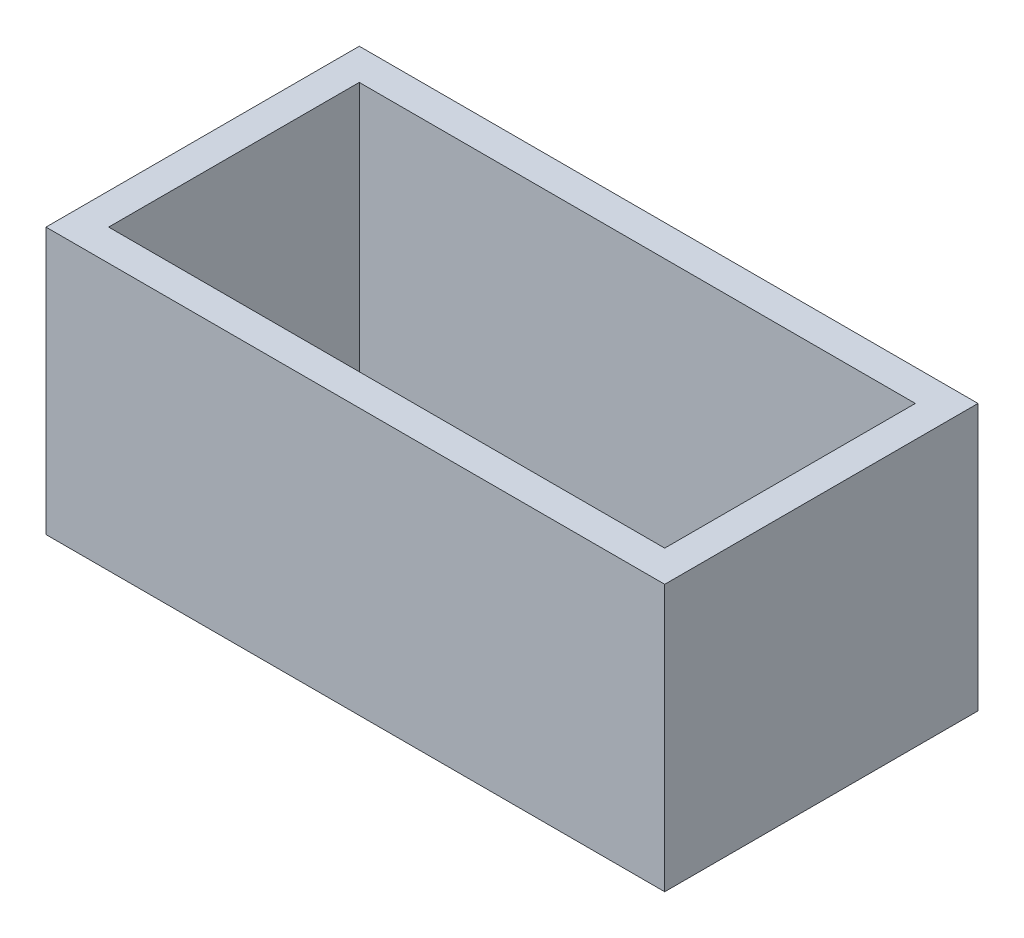
SolidWorks part; units mm, degrees
ref_plane "Front Plane" through (0, 0, 0) normal (0, 0, 1) x (1, 0, 0)
ref_plane "Top Plane" through (0, 0, 0) normal (0, 1, 0) x (1, 0, 0)
ref_plane "Right Plane" through (0, 0, 0) normal (1, 0, 0) x (0, 0, -1)
sketch "Sketch1" plane through (0, 0, 0) normal (0, 1, 0) x (1, 0, 0)
  line L0 (-19.75, -10) -> (-19.75, 10)
  line L1 (17.75, -8) -> (-17.75, -8)
  line L2 (17.75, -8) -> (17.75, 8)
  line L3 (17.75, 8) -> (-17.75, 8)
  line L4 (-17.75, -8) -> (-17.75, 8)
  line L5 (17.75, -8) -> (-17.75, 8) construction
  line L6 (17.75, 8) -> (-17.75, -8) construction
  line L7 (19.75, 10) -> (-19.75, 10)
  line L8 (19.75, -10) -> (19.75, 10)
  line L9 (19.75, -10) -> (-19.75, -10)
  point P0 (0, 0)
  dimension "D1" = 35.5
  dimension "D2" = 16
  dimension "D3" = 2
extrude "Boss-Extrude1" add sketch "Sketch1" along normal blind 17
